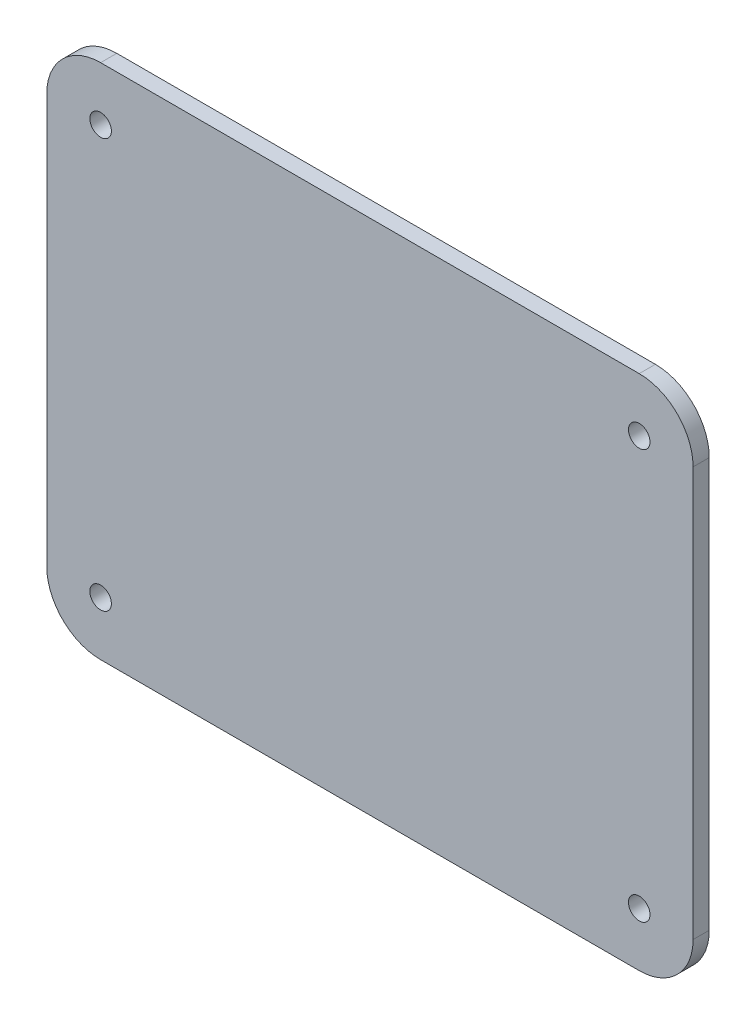
SolidWorks part; units mm, degrees
ref_plane "Front Plane" through (0, 0, 0) normal (0, 0, 1) x (1, 0, 0)
ref_plane "Top Plane" through (0, 0, 0) normal (0, 1, 0) x (1, 0, 0)
ref_plane "Right Plane" through (0, 0, 0) normal (1, 0, 0) x (0, 0, -1)
sketch "Sketch1" plane through (0, 0, 0) normal (0, 0, 1) x (1, 0, 0)
  line L1 (-50, 48) -> (50, 48)
  line L2 (-60, 38) -> (-60, -38)
  line L3 (-50, -48) -> (50, -48)
  line L4 (60, 38) -> (60, -38)
  line L5 (-60, 48) -> (-56.7373, 45.3898) construction
  line L6 (-60, -48) -> (-56.7373, -45.3898) construction
  line L28 (56.7373, -45.3898) -> (60, -48) construction
  line L30 (56.7373, 45.3898) -> (60, 48) construction
  arc A4 (-50, 48) -> (-60, 38) centre (-50, 38) ccw
  arc A5 (-60, -38) -> (-50, -48) centre (-50, -38) ccw
  arc A6 (50, -48) -> (60, -38) centre (50, -38) ccw
  arc A7 (50, 48) -> (60, 38) centre (50, 38) cw
  circle A24 centre (-50, 38) radius 2
  circle A25 centre (50, 38) radius 2
  circle A26 centre (50, -38) radius 2
  circle A27 centre (-50, -38) radius 2
  point P0 (0, 0)
  point P27 (0, 0)
  point P46 (0, 0)
  point P47 (0, 0)
  point P48 (0, 0)
  point P60 (13.1341, -38)
  point P61 (0, 0)
  point P62 (12.9583, -38)
  point P63 (32, -38)
  point P64 (0, 0)
  point P65 (17.3519, -38)
  point P66 (0, 0)
  point P67 (0, 0)
  point P68 (0, 0)
  point P69 (0, 0)
  point P74 (0, 0)
  point P75 (0, 0)
  point P76 (0, 0)
  point P86 (-178.3453, 50.793)
  dimension "D3" = 10
  dimension "D1" = 120
  dimension "D2" = 96
extrude "Boss-Extrude1" add sketch "Sketch1" along normal blind 3
